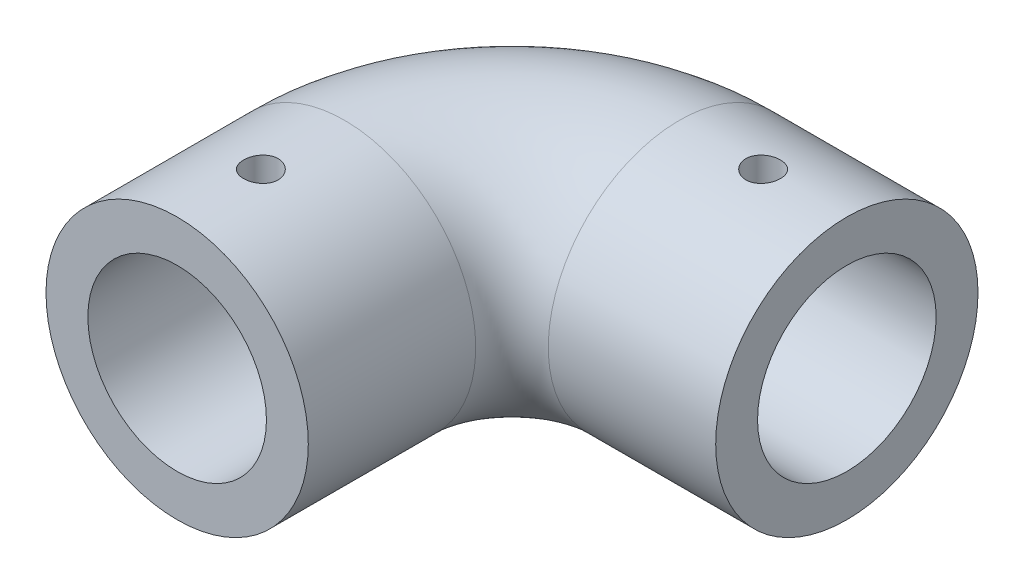
SolidWorks part; units mm, degrees
ref_plane "Front Plane" through (0, 0, 0) normal (0, 0, 1) x (1, 0, 0)
ref_plane "Top Plane" through (0, 0, 0) normal (0, 1, 0) x (1, 0, 0)
ref_plane "Right Plane" through (0, 0, 0) normal (1, 0, 0) x (0, 0, -1)
sketch "Sketch1" plane through (0, 0, 0) normal (0, 1, 0) x (1, 0, 0)
  line L0 (0, 0) -> (0, 30)
  line L1 (30, 60) -> (60, 60)
  arc A0 (0, 30) -> (30, 60) centre (30, 30) cw
  point P6 (0, 60)
  point P7 (0, 0)
  point P8 (0, 0)
  point P9 (0, 0)
  point P10 (0, 0)
  point P11 (0, 0)
  point P12 (0, 0)
  point P13 (0, 0)
  dimension "D3" = 30
  dimension "D1" = 60
  dimension "D2" = 60
sketch "Sketch2" plane through (0, 0, 0) normal (0, 0, 1) x (1, 0, 0)
  circle A0 centre (0, 0) radius 16
  circle A1 centre (0, 0) radius 23.5
  dimension "D1" = 32
  dimension "D2" = 7.5
sweep "Sweep8" add profiles "Sketch2" path "Sketch1"
sketch "Sketch3" plane through (0, 0, 0) normal (0, 1, 0) x (1, 0, 0)
  line L0 (30, 60) -> (60, 60) construction
  circle A0 centre (0, 15) radius 3.1
  circle A1 centre (45, 60) radius 3.1
  dimension "D2" = 6.2
  dimension "D4" = 6.2
  dimension "D1" = 15
  dimension "D3" = 15
extrude "Cut-Extrude1" cut sketch "Sketch3" along normal blind 40
equation "\"D2@Sketch1\"=\"D1@Sketch1\""
equation "\"D4@Sketch3\"=\"D2@Sketch3\""
